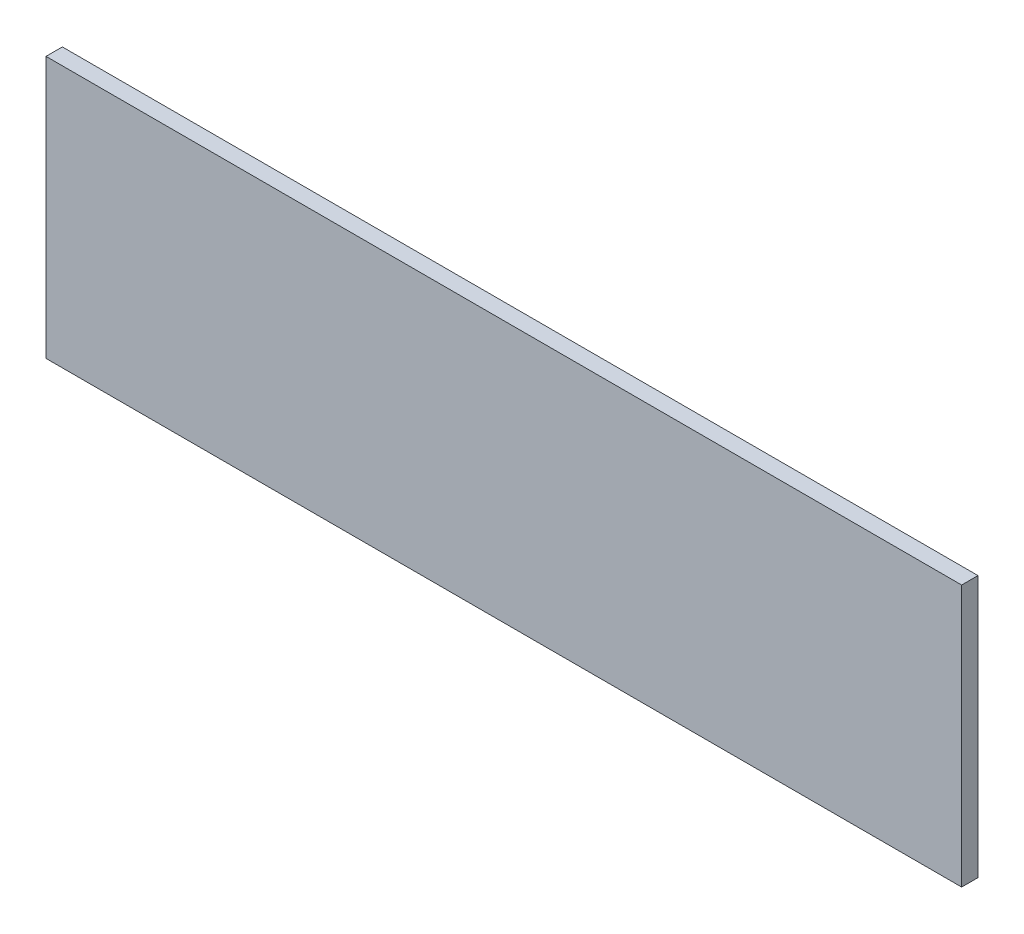
SolidWorks part; units mm, degrees
ref_plane "Front Plane" through (0, 0, 0) normal (0, 0, 1) x (1, 0, 0)
ref_plane "Top Plane" through (0, 0, 0) normal (0, 1, 0) x (1, 0, 0)
ref_plane "Right Plane" through (0, 0, 0) normal (1, 0, 0) x (0, 0, -1)
sketch "Sketch1" plane through (0, 0, 0) normal (0, 0, 1) x (1, 0, 0)
  line L1 (0, 0) -> (177.8, 0)
  line L2 (0, 0) -> (0, 50.8)
  line L3 (0, 50.8) -> (177.8, 50.8)
  line L4 (177.8, 0) -> (177.8, 50.8)
  dimension "D1" = 50.8
  dimension "D2" = 177.8
extrude "Boss-Extrude1" add sketch "Sketch1" along normal blind 3.175
